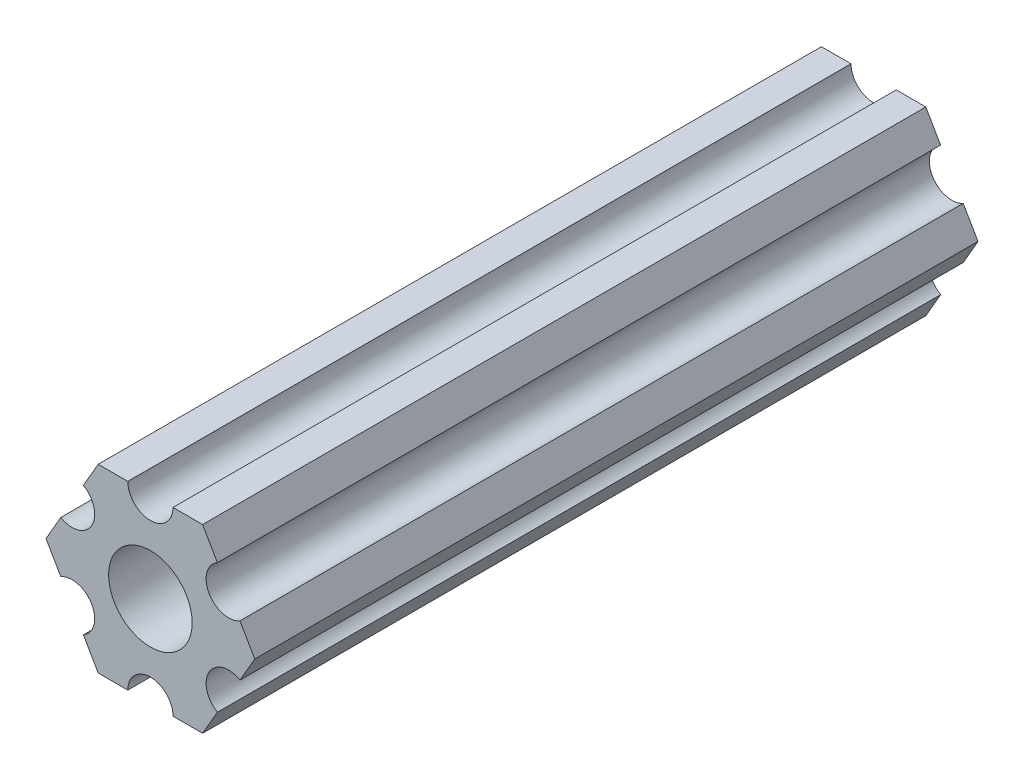
SolidWorks part; units mm, degrees
ref_plane "Front Plane" through (0, 0, 0) normal (0, 0, 1) x (1, 0, 0)
ref_plane "Top Plane" through (0, 0, 0) normal (0, 1, 0) x (1, 0, 0)
ref_plane "Right Plane" through (0, 0, 0) normal (1, 0, 0) x (0, 0, -1)
ref_plane "Plane1" through (0, 0, 0) normal (0, 0, -1) x (-1, 0, 0)
sketch "Sketch1" plane through (0, 0, 0) normal (0, 0, -1) x (-1, 0, 0)
  line L0 (-4.7055, -4.5498) -> (-3.6662, -6.35)
  line L1 (-3.6662, -6.35) -> (-1.5875, -6.35)
  line L2 (1.5875, -6.35) -> (3.6662, -6.35)
  line L3 (3.6662, -6.35) -> (4.7055, -4.5498)
  line L4 (6.293, -1.8002) -> (7.3323, 0)
  line L5 (7.3323, 0) -> (6.293, 1.8002)
  line L6 (4.7055, 4.5498) -> (3.6662, 6.35)
  line L7 (3.6662, 6.35) -> (1.5875, 6.35)
  line L8 (-1.5875, 6.35) -> (-3.6662, 6.35)
  line L9 (-3.6662, 6.35) -> (-4.7055, 4.5498)
  line L10 (-6.293, 1.8002) -> (-7.3323, 0)
  line L11 (-7.3323, 0) -> (-6.293, -1.8002)
  circle A0 centre (0, 0) radius 2.9337
  arc A1 (-6.293, -1.8002) -> (-4.7055, -4.5498) centre (-5.4993, -3.175) cw
  arc A2 (-1.5875, -6.35) -> (1.5875, -6.35) centre (0, -6.35) cw
  arc A3 (4.7055, -4.5498) -> (6.293, -1.8002) centre (5.4993, -3.175) cw
  arc A4 (6.293, 1.8002) -> (4.7055, 4.5498) centre (5.4993, 3.175) cw
  arc A5 (1.5875, 6.35) -> (-1.5875, 6.35) centre (0, 6.35) cw
  arc A6 (-4.7055, 4.5498) -> (-6.293, 1.8002) centre (-5.4993, 3.175) cw
extrude "Boss-Extrude1" add sketch "Sketch1" against normal blind 50.8
